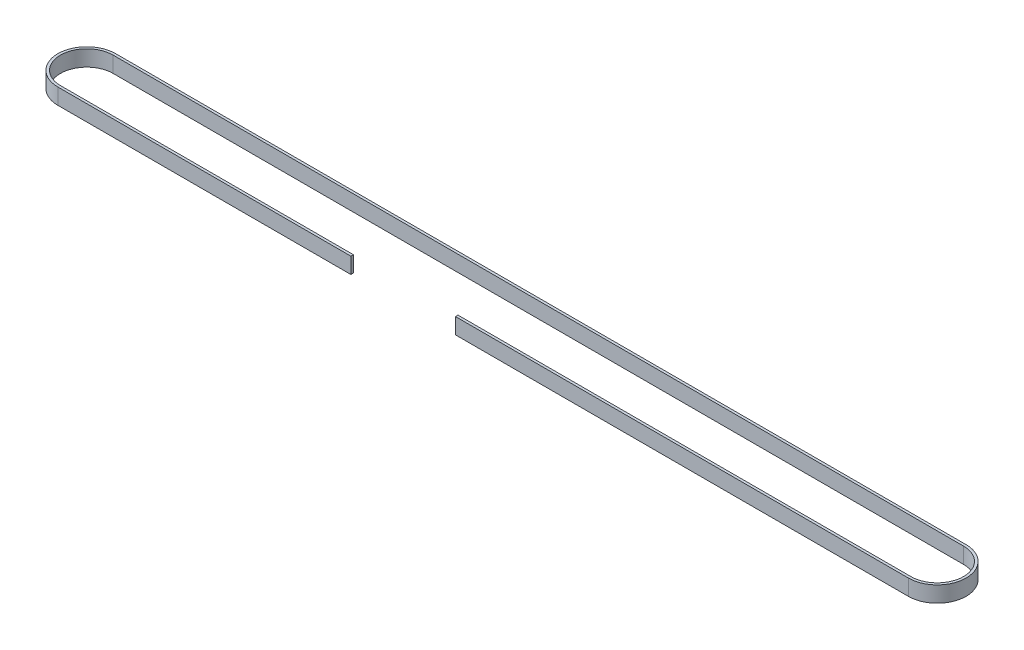
SolidWorks part; units mm, degrees
material "Rubber"
ref_plane "Front Plane" through (0, 0, 0) normal (0, 0, 1) x (1, 0, 0)
ref_plane "Top Plane" through (0, 0, 0) normal (0, 1, 0) x (1, 0, 0)
ref_plane "Right Plane" through (0, 0, 0) normal (1, 0, 0) x (0, 0, -1)
sketch "Sketch1" plane through (0, 0, 0) normal (0, 1, 0) x (1, 0, 0)
  line L0 (0, 16.256) -> (516.128, 16.256)
  line L3 (0, 17.78) -> (516.128, 17.78)
  line L4 (0, -17.272) -> (516.128, -17.272)
  line L5 (0, -15.748) -> (516.128, -15.748)
  arc A2 (516.128, -17.272) -> (516.128, 17.78) centre (516.128, 0.254) ccw
  arc A3 (0, 17.78) -> (0, -17.272) centre (0, 0.254) ccw
  arc A4 (516.128, -15.748) -> (516.128, 16.256) centre (516.128, 0.254) ccw
  arc A5 (0, 16.256) -> (0, -15.748) centre (0, 0.254) ccw
  dimension "D2" = 516.128
  dimension "D3" = 16.002
  dimension "D4" = 16.002
  dimension "D1" = 1.524
extrude "Boss-Extrude1" add sketch "Sketch1" along normal blind 9.652
sketch "Sketch2" plane through (0, 0, 17.272) normal (0, 0, 1) x (1, 0, 0)
  line L0 (0, 9.652) -> (516.128, 9.652) construction
  line L1 (177.8, 9.652) -> (241.3, 9.652)
  line L2 (177.8, 9.652) -> (177.8, 0)
  line L3 (177.8, 0) -> (241.3, 0)
  line L4 (241.3, 9.652) -> (241.3, 0)
  line L5 (0, 0) -> (516.128, 0) construction
  point P4 (241.3, 4.826)
  dimension "D1" = 63.5
  dimension "D2" = 177.8
extrude "Cut-Extrude1" cut sketch "Sketch2" against normal blind 12.7
